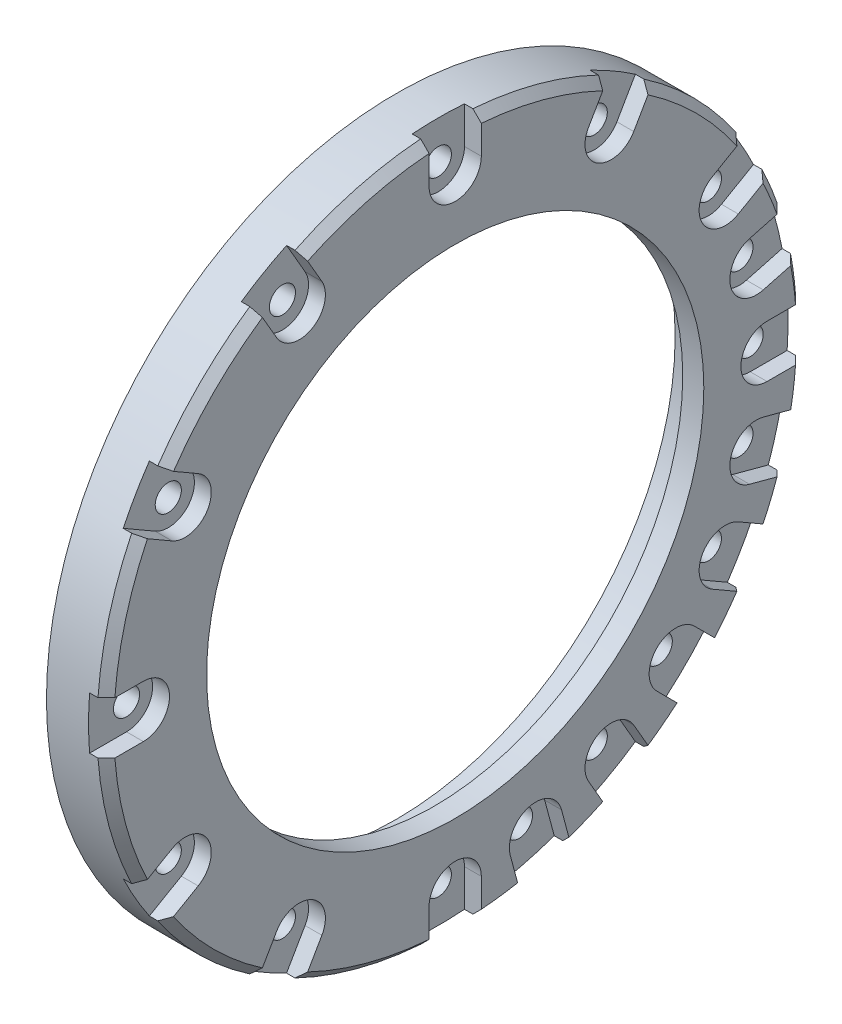
SolidWorks part; units mm, degrees
material "6061 合金"
ref_plane "前视基准面" through (0, 0, 0) normal (0, 0, 1) x (1, 0, 0)
ref_plane "上视基准面" through (0, 0, 0) normal (0, 1, 0) x (1, 0, 0)
ref_plane "右视基准面" through (0, 0, 0) normal (1, 0, 0) x (0, 0, -1)
sketch "草图1" plane through (0, 0, 0) normal (1, 0, 0) x (0, 0, -1)
  circle A0 centre (0, 0) radius 33.1
  circle A1 centre (0, 0) radius 41.5
  dimension "D1" = 66.2
  dimension "D2" = 83
extrude "凸台-拉伸1" add sketch "草图1" along normal blind 7
sketch "草图2" plane through (0, 0, 0) normal (-1, 0, 0) x (0, 0, 1)
  line L0 (0, 37) -> (0, 0) construction
  circle A0 centre (0, 37) radius 1.55
  dimension "D2" = 3.1
  dimension "D1" = 37
extrude "切除-拉伸1" cut sketch "草图2" against normal blind 8
pattern_circular "阵列(圆周)1" count 12 over 360 about axis through (0, 0, 0) along (1, 0, 0) of "切除-拉伸1"
sketch "草图3" plane through (7, 0, 0) normal (1, 0, 0) x (0, 0, -1)
  circle A0 centre (0, 0) radius 33.1
  circle A1 centre (0, 0) radius 29.5
  dimension "D1" = 66.2
  dimension "D2" = 59
extrude "凸台-拉伸2" add sketch "草图3" against normal blind 2.5
chamfer "倒角1" distance 1 angle 45 1 edges at (7, 0, -41.5)
sketch "草图4" plane through (7, 0, 0) normal (1, 0, 0) x (0, 0, -1)
  line L0 (37, 0) -> (41.5, 0) construction
  line L1 (37, 3.1) -> (41.5, 3.1)
  line L2 (37, -3.1) -> (41.5, -3.1)
  circle A1 centre (37, 0) radius 1.55 construction
  arc A5 (37, 3.1) -> (37, -3.1) centre (37, 0) ccw
  arc A6 (41.5, -3.1) -> (41.5, 3.1) centre (41.5, 0) ccw
  circle A7 centre (0, 0) radius 41.5 construction
  point P2 (39.25, 0)
  dimension "D1" = 3.1
extrude "切除-拉伸8" cut sketch "草图4" against normal blind 2
pattern_circular "阵列(圆周)7" count 12 over 360 about axis through (0, 0, 0) along (1, 0, 0) of "切除-拉伸8"
sketch "草图5" [suppressed] plane through (0, 0, 0) normal (1, 0, 0) x (0, 0, -1)
  line L0 (0, 0) -> (0, -37) construction
  line L1 (0, 0) -> (-26.163, -26.163) construction
  circle A0 centre (-26.163, -26.163) radius 3
  circle A1 centre (-26.163, -26.163) radius 1.5
  circle A2 centre (0, -37) radius 1.55 construction
  dimension "D1" = 6
  dimension "D2" = 3
  dimension "D3" = 37
  dimension "D4" = 45
sketch "草图7" plane through (0, 0, 0) normal (-1, 0, 0) x (0, 0, 1)
  line L0 (0, -37) -> (0, 0) construction
  line L1 (0, 0) -> (-9.5763, -35.7393) construction
  circle A0 centre (0, 0) radius 37 construction
  circle A1 centre (0, 0) radius 33.1 construction
  circle A2 centre (-9.5763, -35.7393) radius 1.6
  dimension "D1" = 74
  dimension "D3" = 3.2
  dimension "D2" = 15
extrude "切除-拉伸10" cut sketch "草图7" against normal blind 10
pattern_circular "阵列(圆周)9" count 4 every 30 about axis through (0, 0, 0) along (1, 0, 0) of "切除-拉伸10"
sketch "草图6" plane through (0, 0, 0) normal (-1, 0, 0) x (0, 0, 1)
  circle A0 centre (-9.5763, -35.7393) radius 3
  circle A1 centre (-9.5763, -35.7393) radius 1.6 construction
  dimension "D1" = 6
extrude "切除-拉伸9" cut sketch "草图6" against normal blind 3.5
pattern_circular "阵列(圆周)8" count 4 every 30 about axis through (0, 0, 0) along (1, 0, 0) of "切除-拉伸9"
sketch "草图8" plane through (7, 0, 0) normal (1, 0, 0) x (0, 0, -1)
  line L0 (34.924, 12.619) -> (40.7195, 14.1719)
  line L1 (40.7195, 14.1719) -> (42.3501, 8.0866)
  line L2 (42.3501, 8.0866) -> (36.5545, 6.5336)
  line L3 (0, 0) -> (35.7393, 9.5763) construction
  circle A0 centre (35.7393, 9.5763) radius 3.15
  circle A1 centre (35.7393, 9.5763) radius 1.6 construction
  dimension "D1" = 6.3
  dimension "D2" = 6
extrude "切除-拉伸11" cut sketch "草图8" against normal up to surface (2 mm away)
pattern_circular "阵列(圆周)10" count 4 every 30 about axis through (0, 0, 0) along (1, 0, 0) of "切除-拉伸11"
